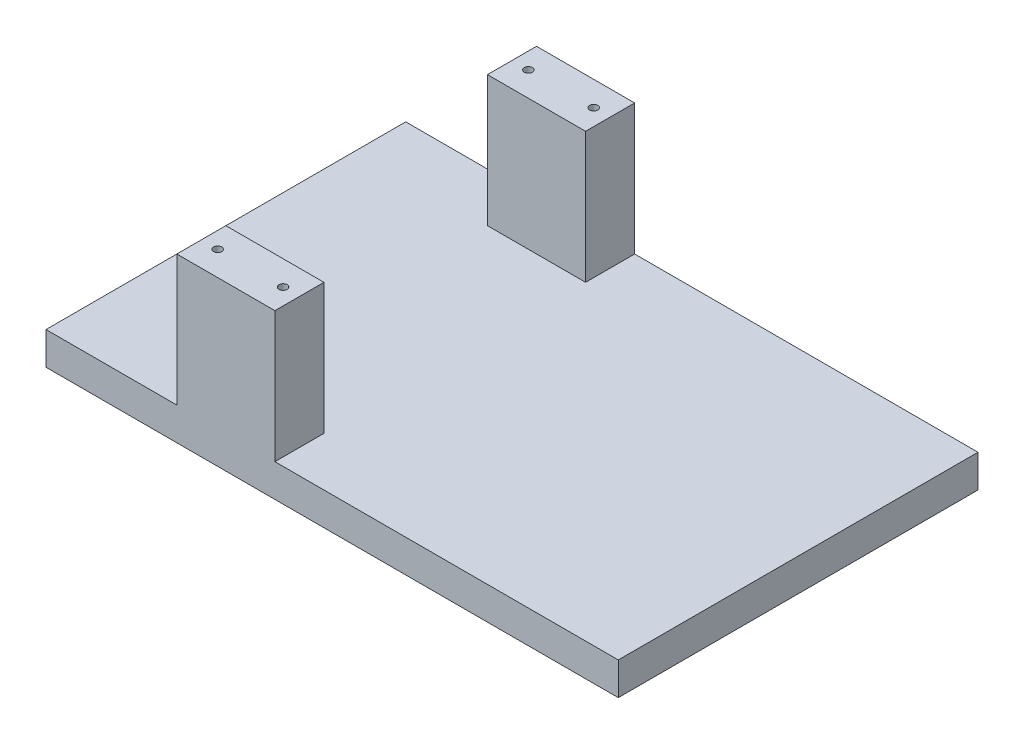
SolidWorks part; units mm, degrees
ref_plane "Front Plane" through (0, 0, 0) normal (0, 0, 1) x (1, 0, 0)
ref_plane "Top Plane" through (0, 0, 0) normal (0, 1, 0) x (1, 0, 0)
ref_plane "Right Plane" through (0, 0, 0) normal (1, 0, 0) x (0, 0, -1)
sketch "Sketch1" plane through (0, 0, 0) normal (0, 1, 0) x (1, 0, 0)
  line L1 (0, 0) -> (175, 0)
  line L2 (0, 0) -> (0, 110)
  line L3 (0, 110) -> (175, 110)
  line L4 (175, 0) -> (175, 110)
extrude "Boss-Extrude1" add sketch "Sketch1" along normal blind 10
sketch "Sketch3" plane through (0, 10, 0) normal (0, 1, 0) x (1, 0, 0)
  line L0 (0, 0) -> (175, 0) construction
  line L1 (40, 0) -> (70, 0)
  line L2 (40, 0) -> (40, 15)
  line L3 (40, 15) -> (70, 15)
  line L4 (70, 0) -> (70, 15)
  line L5 (175, 110) -> (0, 110) construction
  line L6 (40, 110) -> (70, 110)
  line L7 (40, 110) -> (40, 95)
  line L8 (40, 95) -> (70, 95)
  line L9 (70, 110) -> (70, 95)
extrude "Boss-Extrude2" add sketch "Sketch3" along normal blind 40
hole_wizard "M3x0.5 Tapped Hole1" positions "Sketch5" profile "Sketch4" tap size "M3x0.5" standard "Ansi Metric"
sketch "Sketch5" plane through (0, 50, 0) normal (0, 1, 0) x (-1, 0, 0)
  point P0 (-45, -7.5)
  point P1 (-65, -7.5)
  point P3 (-45, -102.5)
  point P5 (-65, -102.5)
sketch "Sketch4" plane through (45, 50, -7.5) normal (1, 0, 0) x (0, 0, 1)
  line L0 (0, 0) -> (0, 8.2511)
  line L1 (0, 8.2511) -> (1.25, 7.5)
  line L2 (1.25, 7.5) -> (1.25, 0)
  line L5 (1.25, 0) -> (0, 0)
  line L10 (0, 8.2511) -> (-1.25, 7.5) construction
  line L11 (0, -6.35) -> (0, 107.95) construction
  dimension "Tap Drill Dia." = 2.5
  dimension "Tap Drill Depth" = 7.5
  dimension "Drill Angle" = 118
cosmetic thread "Hole Thread1"
cosmetic thread "Hole Thread2"
cosmetic thread "Hole Thread3"
cosmetic thread "Hole Thread4"
